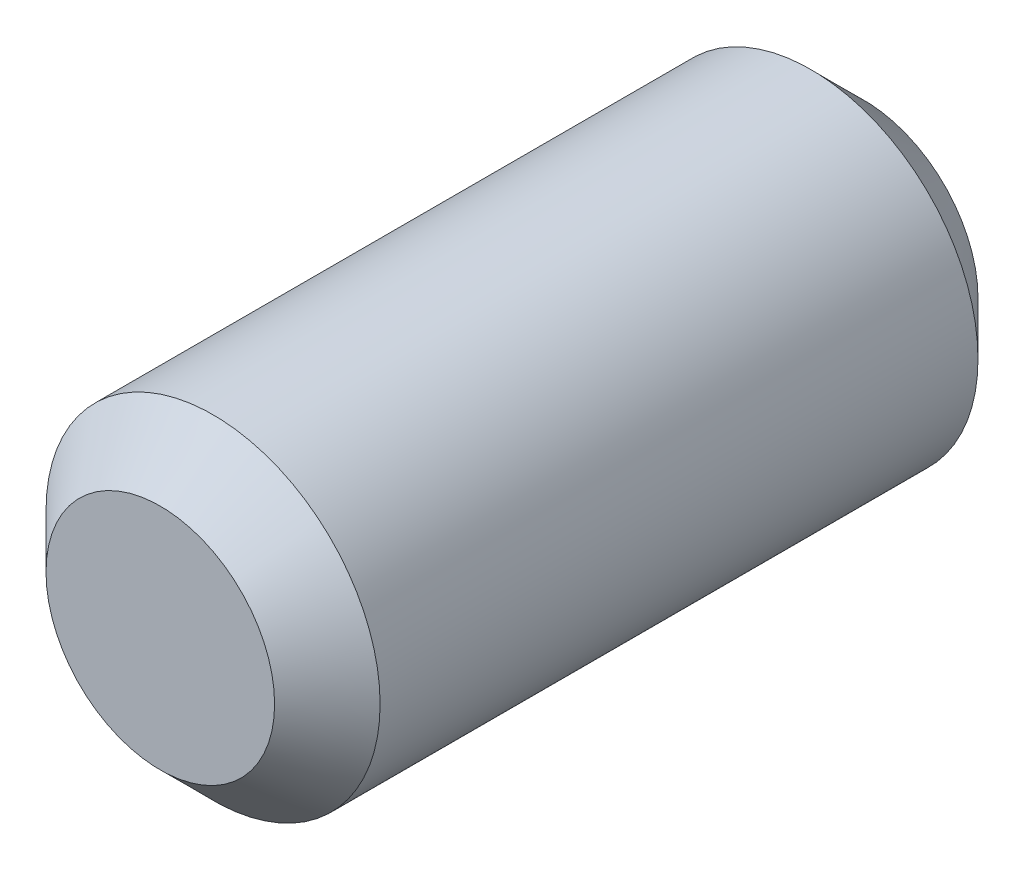
SolidWorks part; units mm, degrees
ref_plane "Front Plane" through (0, 0, 0) normal (1, 0, 0) x (0, 1, 0)
ref_plane "Top Plane" through (0, 0, 0) normal (0, 0, 1) x (0, 1, 0)
ref_plane "Right Plane" through (0, 0, 0) normal (0, 1, 0) x (-1, 0, 0)
sketch "Sketch1" plane through (0, 0, 0) normal (0, 0, 1) x (0, 1, 0)
  circle A0 centre (0, 0) radius 4.75
  dimension "D1" = 9.5
extrude "Boss-Extrude1" add sketch "Sketch1" along normal blind 20
chamfer "Chamfer1" distance 1.5 angle 45 1 edges at (4.75, 0, 0)
chamfer "Chamfer2" distance 1.5 angle 45 1 edges at (4.75, 0, 20)
scale "Scale1" scale about centroid uniform scaling yes scale factor 0.75
scale "Scale2" scale about centroid uniform scaling yes scale factor 0.85
